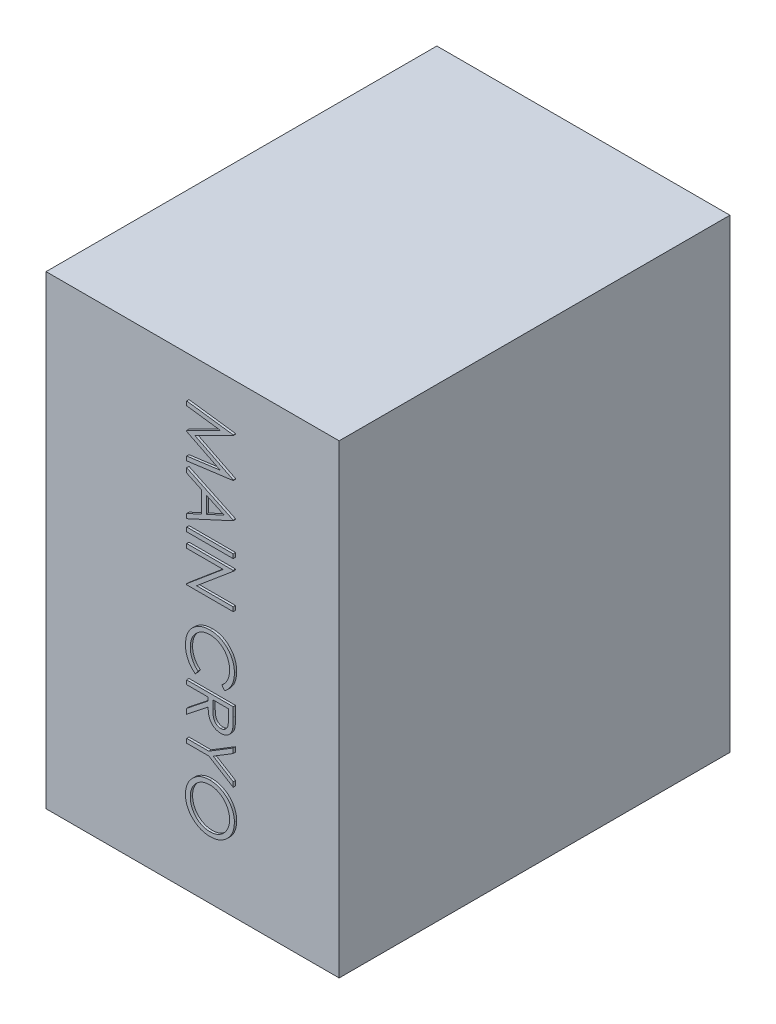
SolidWorks part; units mm, degrees
ref_plane "Front Plane" through (0, 0, 0) normal (0, 0, 1) x (1, 0, 0)
ref_plane "Top Plane" through (0, 0, 0) normal (0, 1, 0) x (1, 0, 0)
ref_plane "Right Plane" through (0, 0, 0) normal (1, 0, 0) x (0, 0, -1)
sketch "Sketch1" plane through (0, 0, 0) normal (0, 0, 1) x (1, 0, 0)
  line L1 (0, 0) -> (-630, 0)
  line L2 (0, 0) -> (0, -1000)
  line L3 (0, -1000) -> (-630, -1000)
  line L4 (-630, 0) -> (-630, -1000)
  dimension "D1" = 630
  dimension "D2" = 1000
extrude "Boss-Extrude1" add sketch "Sketch1" along normal blind 840
sketch "Sketch2" plane through (0, 0, 840) normal (0, 0, 1) x (1, 0, 0)
  line L0 (-322.7594, 0) -> (-322.7594, -1000) construction
  line L1 (0, 0) -> (-630, 0) construction
  line L2 (-630, -1000) -> (0, -1000) construction
  text T0 "  MAIN CRYO" font "Century Gothic" height 100
extrude "Boss-Extrude2" add sketch "Sketch2" along normal blind 5
